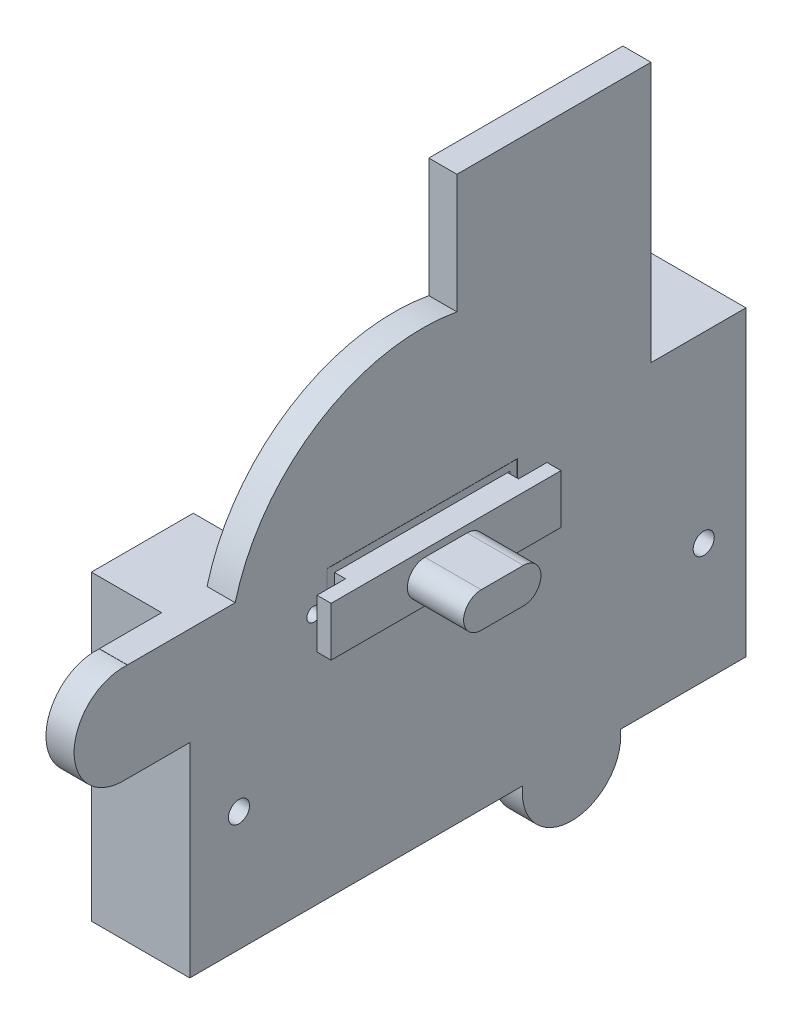
SolidWorks part; units mm, degrees
ref_plane "Front Plane" through (0, 0, 0) normal (0, 0, 1) x (1, 0, 0)
ref_plane "Top Plane" through (0, 0, 0) normal (0, 1, 0) x (1, 0, 0)
ref_plane "Right Plane" through (0, 0, 0) normal (1, 0, 0) x (0, 0, -1)
sketch "Sketch1" plane through (0, 0, 0) normal (1, 0, 0) x (0, 0, -1)
  line L0 (0, 0) -> (33.05, 0) construction
  line L1 (0, 0) -> (-33.05, 0) construction
  line L3 (39.05, 17) -> (-40.05, 17) construction
  line L4 (39.05, 17) -> (39.05, -17)
  line L5 (39.05, -17) -> (-40.05, -17)
  line L6 (-40.05, 17) -> (-40.05, -17)
  line L7 (39.05, 17) -> (-40.05, -17) construction
  line L8 (39.05, -17) -> (-40.05, 17) construction
  line L9 (-40.05, 17) -> (39.05, 17) construction
  line L10 (-40.05, 17) -> (-40.05, 26)
  line L11 (-40.05, 26) -> (39.05, 26)
  line L12 (39.05, 17) -> (39.05, 26)
  circle A0 centre (-33.05, 0) radius 1.5
  circle A1 centre (33.05, 0) radius 1.5
  point P6 (-0.5, 0)
  dimension "D1" = 66.1
  dimension "D2" = 3
  dimension "D3" = 7
  dimension "D4" = 6
  dimension "D5" = 17
  dimension "D6" = 26
extrude "Boss-Extrude1" add sketch "Sketch1" along normal blind 4
sketch "Sketch2" plane through (4, 0, 0) normal (1, 0, 0) x (0, 0, -1)
  line L0 (0, 0) -> (-7, 0) construction
  line L1 (-7, 0) -> (-7, 19) construction
  line L2 (-40.05, -17) -> (39.05, -17) construction
  line L3 (-20.55, 23.675) -> (6.55, 23.675)
  line L4 (-20.55, 23.675) -> (-20.55, 14.325)
  line L5 (-20.55, 14.325) -> (6.55, 14.325)
  line L6 (6.55, 23.675) -> (6.55, 14.325)
  line L7 (-20.55, 23.675) -> (6.55, 14.325) construction
  line L8 (-20.55, 14.325) -> (6.55, 23.675) construction
  line L9 (39.05, 26) -> (-40.05, 26) construction
  circle A0 centre (33.05, 0) radius 1.5 construction
  dimension "D1" = 9.35
  dimension "D2" = 27.1
  dimension "D3" = 7
  dimension "D4" = 19
  dimension "D5" = 31.325
  dimension "D6" = 2.325
  dimension "D7" = 40.05
extrude "Cut-Extrude1" cut sketch "Sketch2" against normal through all
sketch "Sketch3" plane through (4, 0, 0) normal (1, 0, 0) x (0, 0, -1)
  line L0 (-20.55, 19) -> (-22.4, 19) construction
  line L1 (-20.55, 23.675) -> (-20.55, 14.325) construction
  line L2 (6.55, 19) -> (8.4, 19) construction
  line L3 (6.55, 14.325) -> (6.55, 23.675) construction
  circle A0 centre (-22.4, 19) radius 1
  circle A1 centre (8.4, 19) radius 1
  dimension "D1" = 2
  dimension "D2" = 30.8
extrude "Cut-Extrude2" cut sketch "Sketch3" against normal through all
sketch "Sketch4" plane through (0, 0, 0) normal (-1, 0, 0) x (0, 0, 1)
  line L0 (40.05, -17) -> (-39.05, -17) construction
  line L1 (-39.05, 26) -> (-24.55, 26)
  line L2 (-39.05, 26) -> (-39.05, -17)
  line L3 (-39.05, -17) -> (-24.55, -17)
  line L4 (-24.55, 26) -> (-24.55, -17)
  line L6 (40.05, 26) -> (25.55, 26)
  line L7 (40.05, 26) -> (40.05, -17)
  line L8 (40.05, -17) -> (25.55, -17)
  line L9 (25.55, 26) -> (25.55, -17)
  circle A0 centre (-33.05, 0) radius 1.5 construction
  circle A1 centre (-33.05, 0) radius 1.5
  circle A2 centre (33.05, 0) radius 1.5 construction
  circle A3 centre (33.05, 0) radius 1.5
  dimension "D1" = 14.5
  dimension "D2" = 14.5
extrude "Boss-Extrude2" add sketch "Sketch4" along normal blind 10
sketch "Sketch5" plane through (0, 0, 0) normal (-1, 0, 0) x (0, 0, 1)
  line L0 (-6.55, 19) -> (20.55, 19) construction
  line L1 (-6.55, 14.325) -> (-6.55, 23.675) construction
  line L2 (20.55, 23.675) -> (20.55, 14.325) construction
  line L4 (-10.5, 14.35) -> (24.5, 14.35)
  line L5 (-10.5, 14.35) -> (-10.5, 23.65)
  line L6 (-10.5, 23.65) -> (24.5, 23.65)
  line L7 (24.5, 14.35) -> (24.5, 23.65)
  line L8 (-10.5, 14.35) -> (24.5, 23.65) construction
  line L9 (-10.5, 23.65) -> (24.5, 14.35) construction
  circle A0 centre (-8.4, 19) radius 1 construction
  circle A1 centre (-8.4, 19) radius 1
  circle A2 centre (22.4, 19) radius 1 construction
  circle A3 centre (22.4, 19) radius 1
  point P6 (7, 19)
  dimension "D1" = 35
  dimension "D2" = 9.3
extrude "Boss-Extrude3" add sketch "Sketch5" along normal blind 2 separate body
sketch "Sketch6" plane through (0, 0, 0) normal (1, 0, 0) x (0, 0, -1)
  line L0 (-20.55, 19) -> (6.55, 19) construction
  line L1 (-20.55, 23.675) -> (-20.55, 14.325) construction
  line L2 (6.55, 14.325) -> (6.55, 23.675) construction
  line L3 (10.5, 23.65) -> (10.5, 14.35) construction
  line L4 (-20.5, 14.35) -> (6.5, 14.35)
  line L5 (-20.5, 14.35) -> (-20.5, 23.65)
  line L6 (-20.5, 23.65) -> (6.5, 23.65)
  line L7 (6.5, 14.35) -> (6.5, 23.65)
  line L8 (-20.5, 14.35) -> (6.5, 23.65) construction
  line L9 (-20.5, 23.65) -> (6.5, 14.35) construction
  line L10 (-19.5, 22.65) -> (5.5, 22.65)
  line L11 (5.5, 15.35) -> (5.5, 22.65)
  line L12 (-19.5, 15.35) -> (5.5, 15.35)
  line L13 (-19.5, 15.35) -> (-19.5, 22.65)
  point P6 (-7, 19)
  dimension "D1" = 27
  dimension "D2" = 1
extrude "Boss-Extrude4" add sketch "Sketch6" along normal blind 4
sketch "Sketch7" plane through (-2, 0, 0) normal (-1, 0, 0) x (0, 0, 1)
  line L0 (-10.5, 19) -> (24.5, 19) construction
  line L1 (-10.5, 23.65) -> (-10.5, 14.35) construction
  line L2 (24.5, 14.35) -> (24.5, 23.65) construction
  line L3 (4, 19) -> (10, 19) construction
  line L4 (4, 21.5) -> (10, 21.5)
  line L5 (4, 16.5) -> (10, 16.5)
  arc A0 (4, 21.5) -> (4, 16.5) centre (4, 19) ccw
  arc A1 (10, 16.5) -> (10, 21.5) centre (10, 19) ccw
  point P8 (7, 19)
  dimension "D2" = 11
  dimension "D1" = 5
extrude "Boss-Extrude5" add sketch "Sketch7" along normal blind 8
sketch "Sketch8" plane through (0, 0, 0) normal (-1, 0, 0) x (0, 0, 1)
  line L0 (-6.55, 23.675) -> (20.55, 23.675) construction
  line L1 (-10.55, 23.675) -> (24.55, 23.675)
  line L2 (20.55, 14.325) -> (-6.55, 14.325) construction
  line L3 (24.55, 14.325) -> (-10.55, 14.325)
  line L4 (-10.5, 14.35) -> (24.5, 14.35) construction
  line L5 (-10.5, 14.35) -> (24.5, 14.35) construction
  line L8 (-10.55, 23.65) -> (-10.55, 14.35)
  line L9 (-10.55, 23.675) -> (-10.55, 14.325)
  line L10 (26.55, 12.325) -> (26.55, 25.675)
  line L11 (24.55, 14.35) -> (24.55, 23.65)
  line L12 (24.55, 14.325) -> (24.55, 23.675)
  line L13 (-12.55, 25.675) -> (26.55, 25.675)
  line L14 (-12.55, 25.675) -> (-12.55, 12.325)
  line L15 (26.55, 12.325) -> (-12.55, 12.325)
  dimension "D1" = 0.025
  dimension "D2" = 0.05
  dimension "D3" = 0.05
  dimension "D4" = 2
extrude "Boss-Extrude6" add sketch "Sketch8" along normal blind 2
sketch "Sketch9" plane through (4, 0, 0) normal (1, 0, 0) x (0, 0, -1)
  line L0 (-19.5, 19) -> (5.5, 19) construction
  line L1 (-19.5, 22.65) -> (-19.5, 15.35) construction
  line L2 (5.5, 15.35) -> (5.5, 22.65) construction
  circle A0 centre (-7, 19) radius 10
  dimension "D1" = 20
sketch "Sketch10" plane through (0, 0, 0) normal (1, 0, 0) x (0, 0, -1)
  line L4 (5.5, 15.35) -> (5.5, 22.65)
  line L5 (5.5, 22.65) -> (-19.5, 22.65)
  line L6 (-19.5, 22.65) -> (-19.5, 15.35)
  line L7 (-19.5, 15.35) -> (5.5, 15.35)
  line L8 (5.5, 15.35) -> (5.5, 22.65)
  line L9 (5.5, 22.65) -> (-19.5, 22.65)
  line L10 (-19.5, 22.65) -> (-19.5, 15.35)
  line L11 (-19.5, 15.35) -> (5.5, 15.35)
  dimension "D1" = 0
extrude "Boss-Extrude7" add sketch "Sketch10" along normal offset from surface (1.3 mm away) 2.7 up to face at (4, 19, 7)
sketch "Sketch11" plane through (1.3, 0, 0) normal (1, 0, 0) x (0, 0, -1)
  line L0 (-19.5, 19) -> (5.5, 19) construction
  line L2 (-19.3, 15.5) -> (5.3, 15.5)
  line L3 (-19.3, 15.5) -> (-19.3, 22.5)
  line L4 (-19.3, 22.5) -> (5.3, 22.5)
  line L5 (5.3, 15.5) -> (5.3, 22.5)
  line L6 (-19.3, 15.5) -> (5.3, 22.5) construction
  line L7 (-19.3, 22.5) -> (5.3, 15.5) construction
  point P4 (-7, 19)
  dimension "D1" = 7
  dimension "D2" = 24.6
extrude "Boss-Extrude8" add sketch "Sketch11" along normal offset from surface (4.1 mm away) 1.4 separate body up to face at (4, 19, 7) offset beyond the face yes
sketch "Sketch12" plane through (5.4, 0, 0) normal (1, 0, 0) x (0, 0, -1)
  line L0 (-19.3, 19) -> (5.3, 19) construction
  line L1 (-19.3, 15.5) -> (-19.3, 22.5) construction
  line L2 (5.3, 22.5) -> (5.3, 15.5) construction
  line L3 (-19.3, 22.5) -> (5.3, 22.5) construction
  line L4 (-23.35, 15.5) -> (9.35, 15.5)
  line L5 (-23.35, 15.5) -> (-23.35, 22.5)
  line L6 (-23.35, 22.5) -> (9.35, 22.5)
  line L7 (9.35, 15.5) -> (9.35, 22.5)
  line L8 (-23.35, 15.5) -> (9.35, 22.5) construction
  line L9 (-23.35, 22.5) -> (9.35, 15.5) construction
  point P6 (-7, 19)
  dimension "D1" = 32.7
extrude "Boss-Extrude9" add sketch "Sketch12" along normal blind 2
sketch "Sketch13" plane through (7.4, 0, 0) normal (1, 0, 0) x (0, 0, -1)
  line L2 (-10, 16.5) -> (-4, 16.5)
  line L3 (-4, 21.5) -> (-10, 21.5)
  line L4 (-10, 16.5) -> (-4, 16.5)
  line L5 (-4, 21.5) -> (-10, 21.5)
  arc A2 (-4, 16.5) -> (-4, 21.5) centre (-4, 19) ccw
  arc A3 (-10, 21.5) -> (-10, 16.5) centre (-10, 19) ccw
  arc A4 (-4, 16.5) -> (-4, 21.5) centre (-4, 19) ccw
  arc A5 (-10, 21.5) -> (-10, 16.5) centre (-10, 19) ccw
  dimension "D1" = 0
extrude "Boss-Extrude10" add sketch "Sketch13" along normal blind 8
sketch "Sketch14" plane through (4, 0, 0) normal (1, 0, 0) x (0, 0, -1)
  line L0 (-100.3042, 63) -> (95.3813, 63) construction
  line L1 (-7, 19) -> (-67.1945, 19) construction
  circle A0 centre (-33.05, 0) radius 1.5 construction
  dimension "D1" = 63
  dimension "D2" = 44
sketch "Sketch15" plane through (4, 0, 0) normal (1, 0, 0) x (0, 0, -1)
  line L0 (25.55, 26) -> (25.55, 63)
  line L1 (39.05, 26) -> (-40.05, 26) construction
  line L2 (25.55, 63) -> (-2.05, 63)
  line L3 (-2.05, 63) -> (-2.05, 26)
  line L4 (-2.05, 26) -> (25.55, 26)
  line L5 (39.05, -17) -> (39.05, 26) construction
  line L6 (-40.05, 26) -> (-40.05, -17) construction
  dimension "D1" = 37
  dimension "D2" = 13.5
  dimension "D3" = 38
extrude "Boss-Extrude11" add sketch "Sketch15" against normal up to surface (4 mm away) up to face at (0, 11.75, 3.5)
sketch "Sketch16" plane through (4, 0, 0) normal (1, 0, 0) x (0, 0, -1)
  line L0 (-2.05, 26) -> (-40.05, 26) construction
  line L1 (-2.05, 26) -> (-40.05, 26)
  line L2 (-2.05, 63) -> (-2.05, 26) construction
  line L3 (-2.05, 63) -> (-2.05, 26)
  circle A0 centre (-7, 19) radius 27.5
  line M15 (-2.05, 26) -> (-40.05, 26)
  dimension "D1" = 55
extrude "Boss-Extrude12" add sketch "Sketch16" against normal up to surface (4 mm away) contours L3 A0 M15
sketch "Sketch17" plane through (4, 0, 0) normal (1, 0, 0) x (0, 0, -1)
  line L0 (-7, 19) -> (14.25, 55.8061) construction
  line L1 (14.25, -17.8061) -> (-7, 19) construction
  line L2 (-7, 19) -> (-49.5, 19) construction
  line L3 (-49.5, 12) -> (-40.05, 12)
  line L4 (-40.05, 26) -> (-40.05, -17) construction
  line L5 (-49.5, 26) -> (-40.05, 26)
  line L6 (-40.05, 26) -> (-40.05, 12)
  line L7 (20.3122, -14.3061) -> (13.1235, -1.8549)
  line L8 (8.1878, -21.3061) -> (-0.9968, -5.3978)
  line L9 (8.1878, 59.3061) -> (0.8574, 46.6093)
  line L10 (20.3122, 52.3061) -> (12.809, 39.3102)
  line L11 (-33.5942, 26) -> (-40.05, 26) construction
  line L12 (-40.05, -17) -> (39.05, -17) construction
  line L13 (-40.05, -17) -> (39.05, -17)
  line L14 (14.25, 55.8061) -> (56.1042, 55.8061) construction
  line L15 (39.05, 26) -> (25.55, 26) construction
  arc A0 (-2.05, 46.0508) -> (-33.5942, 26) centre (-7, 19) ccw construction
  circle A1 centre (-7, 19) radius 27.5
  circle A2 centre (-7, 19) radius 42.5
  circle A3 centre (14.25, -17.8061) radius 7
  circle A4 centre (14.25, 55.8061) radius 7
  circle A5 centre (-49.5, 19) radius 7
  line M15 (-40.05, 26) -> (-40.05, -17)
  dimension "D3" = 85
  dimension "D4" = 29.8061
  dimension "D1" = 120
  dimension "D2" = 120
extrude "Boss-Extrude13" add sketch "Sketch17" against normal up to surface (4 mm away) contours A2 A5 | A2 A5 | A5 A2 L3 L5 M15 | L13 A3 A2 | A2 A3 L13
